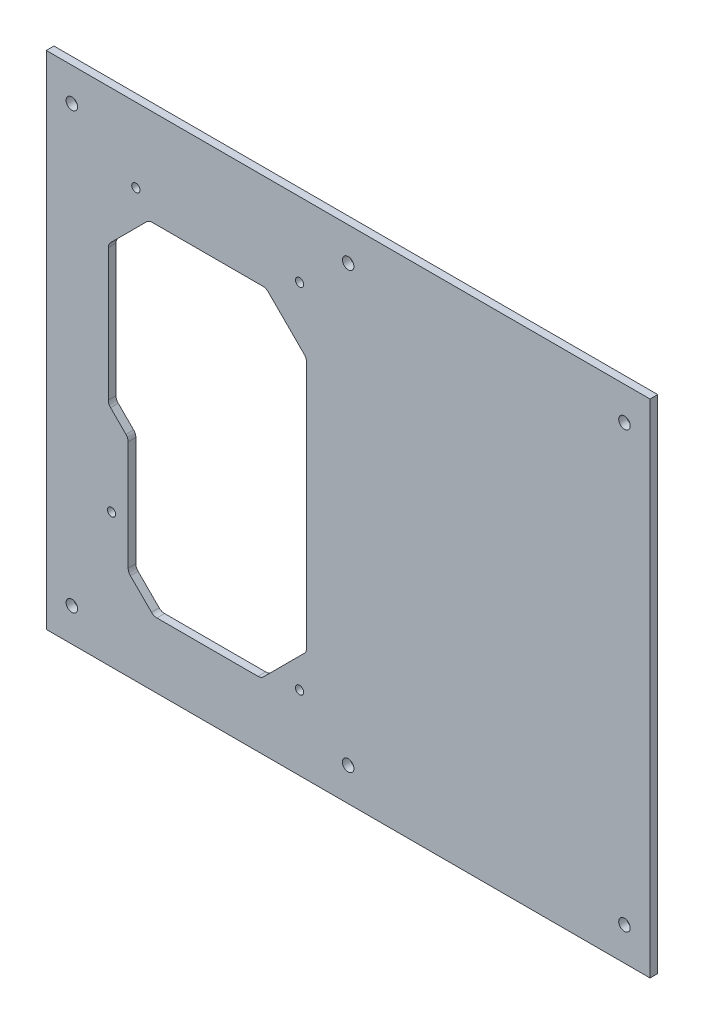
SolidWorks part; units mm, degrees
ref_plane "Спереди" through (0, 0, 0) normal (0, 0, 1) x (1, 0, 0)
ref_plane "Сверху" through (0, 0, 0) normal (0, 1, 0) x (1, 0, 0)
ref_plane "Справа" through (0, 0, 0) normal (1, 0, 0) x (0, 0, -1)
sketch "Эскиз1" plane through (0, 0, 0) normal (0, 0, 1) x (1, 0, 0)
  line L0 (0, 0) -> (236, 0)
  line L1 (0, 0) -> (0, 196)
  line L2 (236, 0) -> (236, 196)
  line L3 (0, 196) -> (236, 196)
  line L4 (10, 183) -> (226, 183) construction
  line L5 (10, 183) -> (10, 13) construction
  line L6 (226, 183) -> (226, 13) construction
  line L7 (10, 13) -> (226, 13) construction
  circle A0 centre (10, 183) radius 2.25
  circle A1 centre (10, 13) radius 2.25
  circle A2 centre (226, 183) radius 2.25
  circle A3 centre (226, 13) radius 2.25
  circle A4 centre (118, 183) radius 2.25
  circle A5 centre (118, 13) radius 2.25
  dimension "D7" = 4.5
  dimension "D8" = 4.5
  dimension "D9" = 4.5
  dimension "D10" = 4.5
  dimension "D11" = 4.5
  dimension "D12" = 4.5
  dimension "D1" = 236
  dimension "D2" = 196
  dimension "D3" = 10
  dimension "D4" = 13
  dimension "D5" = 10
  dimension "D6" = 13
extrude "Бобышка-Вытянуть1" add sketch "Эскиз1" along normal blind 3
sketch "Эскиз4" plane through (0, 0, 3) normal (0, 0, 1) x (1, 0, 0)
  circle A0 centre (35, 167) radius 2.25 construction
  circle A1 centre (35, 167) radius 2.25
  circle A2 centre (99, 167) radius 2.25 construction
  circle A3 centre (99, 167) radius 2.25
  circle A4 centre (25.5, 52.5) radius 2.25 construction
  circle A5 centre (25.5, 52.5) radius 2.25
  circle A6 centre (99, 29) radius 2.25 construction
  circle A7 centre (99, 29) radius 2.25
sketch "Эскиз2" plane through (0, 0, 0) normal (0, 0, 1) x (1, 0, 0)
  line L0 (0, 196) -> (0, 0) construction
  line L2 (0, 196) -> (0, 0) construction
  line L4 (0, 0) -> (236, 0) construction
  line L5 (236, 196) -> (0, 196) construction
  line L10 (85.8787, 158.5) -> (40.1212, 158.5) construction
  line L11 (101.75, 142.6287) -> (85.8787, 158.5)
  line L12 (42, 25.5) -> (32, 35.5)
  line L14 (40.1212, 158.5) -> (85.8787, 158.5)
  line L15 (24.25, 88.5) -> (24.25, 142.6288)
  line L16 (32, 80.75) -> (24.25, 88.5)
  line L17 (32, 35.5) -> (32, 80.75)
  line L18 (84, 25.5) -> (42, 25.5)
  line L19 (101.75, 43.25) -> (84, 25.5)
  line L20 (101.75, 142.6287) -> (101.75, 43.25)
  line L21 (40.1212, 158.5) -> (24.25, 142.6288)
  circle A1 centre (25.5, 52.5) radius 1.6
  circle A2 centre (99, 29) radius 1.6
  circle A3 centre (35, 167) radius 1.6
  circle A4 centre (99, 167) radius 1.6
  point P1 (99, 167)
  dimension "D8" = 69.75
  dimension "D9" = 135
  dimension "D10" = 45.25
  dimension "D11" = 135
  dimension "D17" = 135
  dimension "D18" = 25.5
  dimension "D23" = 3.2
  dimension "D24" = 3.2
  dimension "D19" = 52.5
  dimension "D20" = 3.2
  dimension "D21" = 29
  dimension "D22" = 99
  dimension "D25" = 29
  dimension "D26" = 35
  dimension "D27" = 29
  dimension "D28" = 3.2
  dimension "D29" = 64
  dimension "D2" = 32
  dimension "D3" = 25.5
  dimension "D4" = 135
  dimension "D5" = 35.5
  dimension "D6" = 135
  dimension "D7" = 43.25
  dimension "D1" = 24.25
  dimension "D12" = 40.1212
  dimension "D13" = 54.1288
  dimension "D15" = 133
  dimension "D16" = 45.7575
  dimension "D14" = 77.5
extrude "Вырез-Вытянуть2" cut sketch "Эскиз2" along normal through all
fillet "Скругление1" radius 3 10 edges at (24.25, 142.6288, 1.5) (40.1212, 158.5, 1.5) (85.8787, 158.5, 1.5) (101.75, 142.6287, 1.5) (101.75, 43.25, 1.5) (84, 25.5, 1.5) (42, 25.5, 1.5) (32, 35.5, 1.5) (32, 80.75, 1.5) (24.25, 88.5, 1.5)
